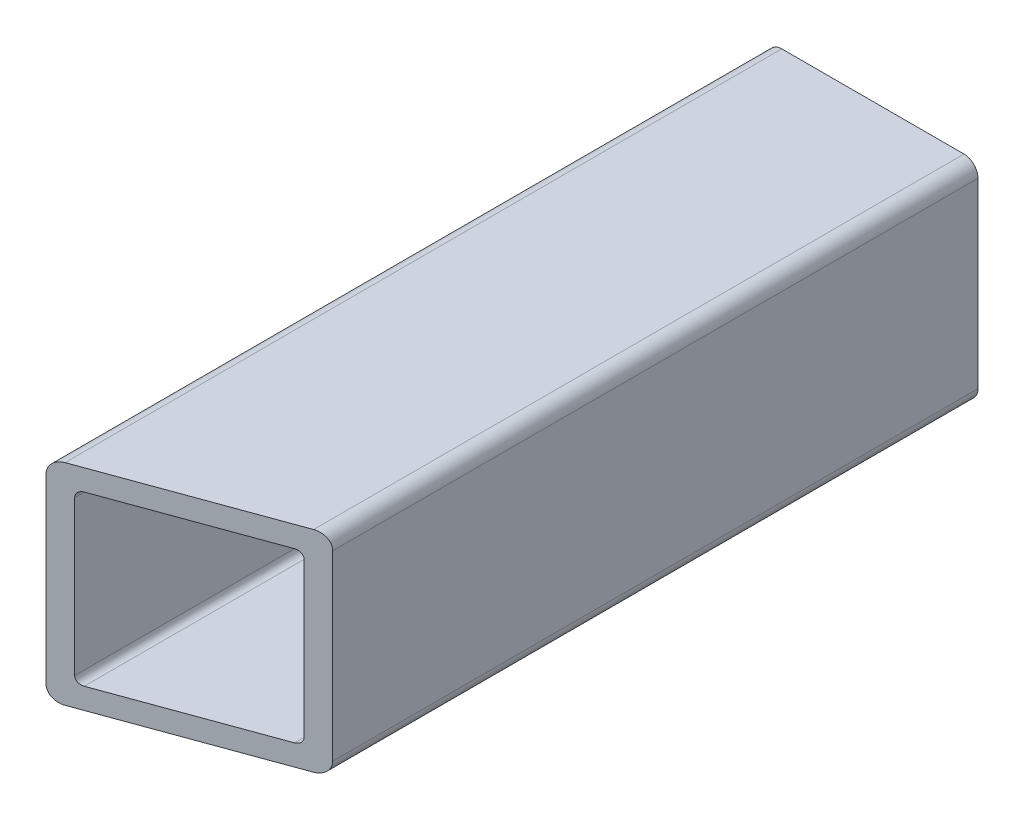
SolidWorks part; units mm, degrees
material "1.0553 (S355J0)"
ref_plane "Płaszczyzna przednia" through (0, 0, 0) normal (0, 0, 1) x (1, 0, 0)
ref_plane "Płaszczyzna górna" through (0, 0, 0) normal (0, 1, 0) x (1, 0, 0)
ref_plane "Płaszczyzna prawa" through (0, 0, 0) normal (1, 0, 0) x (0, 0, -1)
sketch "Szkic1" plane through (0, 0, 0) normal (0, 0, 1) x (1, 0, 0)
  line L0 (-13, -3) -> (13, -3)
  line L1 (-15, -1) -> (-15, 25)
  line L2 (-13, 27) -> (13, 27)
  line L3 (15, -1) -> (15, 25)
  line L4 (-11, 0) -> (11, 0)
  line L5 (-12, 1) -> (-12, 23)
  line L6 (-11, 24) -> (11, 24)
  line L7 (12, 1) -> (12, 23)
  arc A0 (-15, -1) -> (-13, -3) centre (-13, -1) ccw
  arc A1 (13, -3) -> (15, -1) centre (13, -1) ccw
  arc A2 (15, 25) -> (13, 27) centre (13, 25) ccw
  arc A3 (-13, 27) -> (-15, 25) centre (-13, 25) ccw
  arc A4 (-12, 1) -> (-11, 0) centre (-11, 1) ccw
  arc A5 (11, 0) -> (12, 1) centre (11, 1) ccw
  arc A6 (12, 23) -> (11, 24) centre (11, 23) ccw
  arc A7 (-11, 24) -> (-12, 23) centre (-11, 23) ccw
  point P24 (0, 0)
  dimension "D1" = 2
  dimension "D6" = 1
  dimension "D2" = 3
  dimension "D3" = 3
  dimension "D4" = 3
  dimension "D5" = 3
  dimension "D7" = 30
  dimension "D8" = 30
extrude "Dodanie-wyciągnięcie1" add sketch "Szkic1" along normal blind 103
sketch "Szkic2" plane through (0, -3, 0) normal (0, -1, 0) x (1, 0, 0)
  line L0 (-15, 103) -> (66.1563, 73.4615)
  line L1 (-13, 103) -> (13, 103) construction
  line L2 (-15, 103) -> (66.1563, 103)
  line L3 (66.1563, 103) -> (66.1563, 73.4615)
  dimension "D1" = 20
extrude "Wytnij-wyciągnięcie1" cut sketch "Szkic2" against normal blind 70
